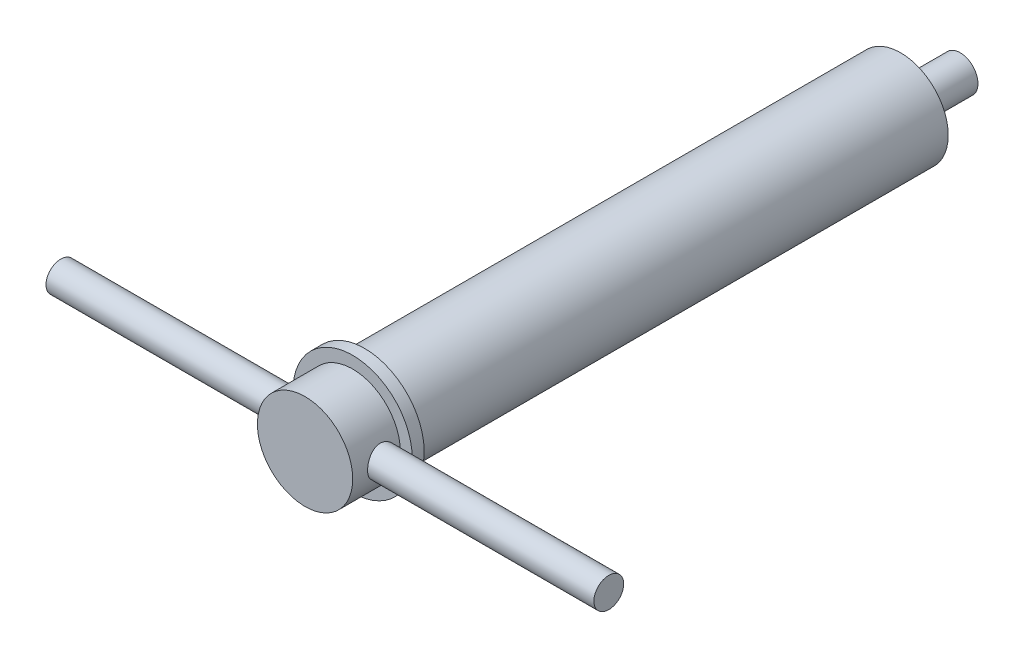
SolidWorks part; units mm, degrees
material "Malleable Cast Iron"
ref_plane "Front Plane" through (0, 0, 0) normal (0, 0, 1) x (1, 0, 0)
ref_plane "Top Plane" through (0, 0, 0) normal (0, 1, 0) x (1, 0, 0)
ref_plane "Right Plane" through (0, 0, 0) normal (1, 0, 0) x (0, 0, -1)
sketch "Sketch1" plane through (0, 0, 0) normal (0, 0, 1) x (1, 0, 0)
  circle A0 centre (0, 0) radius 4
extrude "Boss-Extrude1" add sketch "Sketch1" along normal blind 50
ref_plane "Plane1" through (0, 0, 46) normal (0, 0, 1) x (1, 0, 0)
sketch "Sketch2" plane through (0, 0, 46) normal (0, 0, 1) x (1, 0, 0)
  circle A0 centre (0, 0) radius 5
extrude "Boss-Extrude2" add sketch "Sketch2" against normal blind 1
ref_plane "Plane2" through (0, 0, 0) normal (1, 0, 0) x (0, 0, -1)
sketch "Sketch3" plane through (0, 0, 0) normal (1, 0, 0) x (0, 0, -1)
  line L0 (-50, 4) -> (-50, -4) construction
  circle A0 centre (-47.5, 0) radius 1.25
  dimension "D1" = 2.5
  dimension "D2" = 2.5
extrude "Boss-Extrude3" add sketch "Sketch3" along normal mid plane 46
sketch "Sketch4" plane through (0, 0, 0) normal (0, 0, -1) x (-1, 0, 0)
  circle A0 centre (0, 0) radius 1.5
extrude "Boss-Extrude4" add sketch "Sketch4" along normal blind 5
